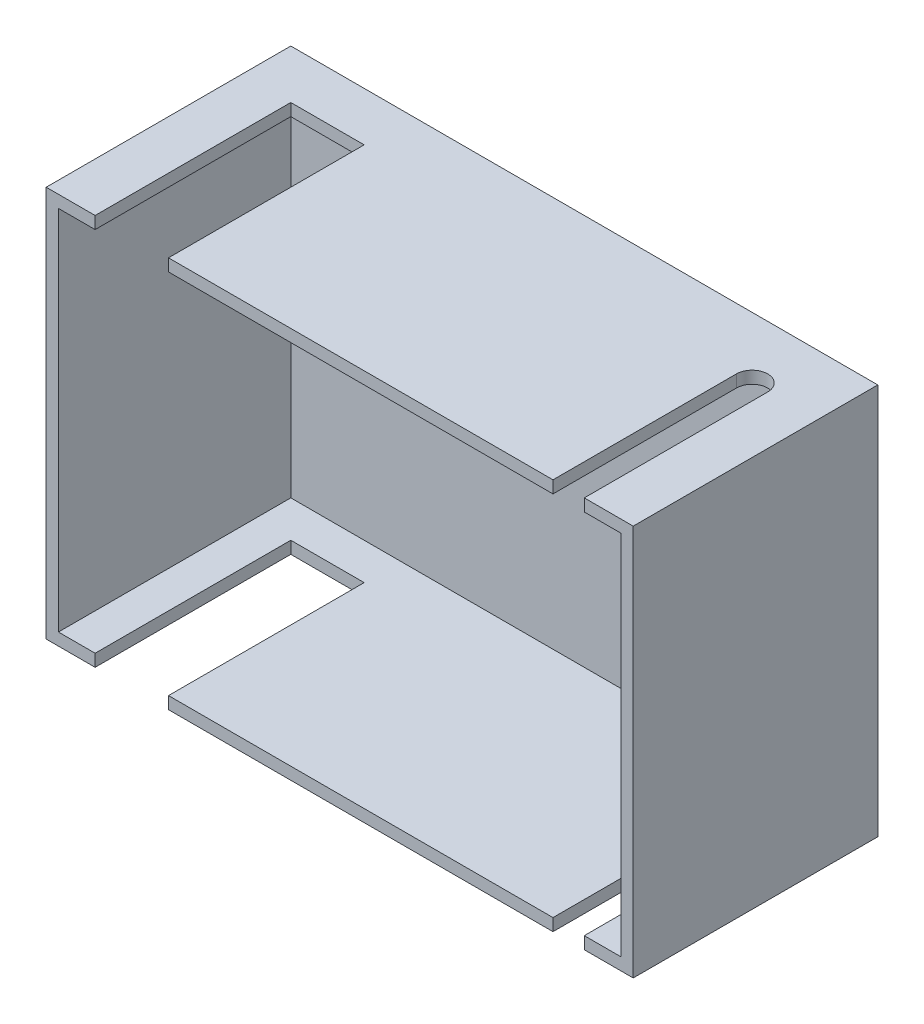
SolidWorks part; units mm, degrees
ref_plane "前基準面" through (0, 0, 0) normal (0, 0, 1) x (1, 0, 0)
ref_plane "上基準面" through (0, 0, 0) normal (0, 1, 0) x (1, 0, 0)
ref_plane "右基準面" through (0, 0, 0) normal (1, 0, 0) x (0, 0, -1)
sketch "草圖1" plane through (0, 0, 0) normal (0, 0, 1) x (1, 0, 0)
  line L1 (-60, 40) -> (60, 40)
  line L2 (-60, 40) -> (-60, -40)
  line L3 (-60, -40) -> (60, -40)
  line L4 (60, 40) -> (60, -40)
  line L5 (-60, 40) -> (60, -40) construction
  line L6 (-60, -40) -> (60, 40) construction
  point P0 (0, 0)
  dimension "D1" = 120
  dimension "D2" = 80
extrude "填料-伸長1" add sketch "草圖1" along normal blind 50
shell "薄殼1" thickness 2.5
sketch "草圖2" plane through (0, -40, 0) normal (0, -1, 0) x (1, 0, 0)
  line L1 (-50, 50) -> (-35, 50)
  line L2 (-50, 50) -> (-50, 10)
  line L3 (-50, 10) -> (-35, 10)
  line L4 (-35, 50) -> (-35, 10)
  line L5 (-50, 50) -> (-35, 10) construction
  line L6 (-50, 10) -> (-35, 50) construction
  line L7 (-60, 50) -> (60, 50) construction
  line L8 (-60, 50) -> (-60, 0) construction
  point P0 (-42.5, 30)
  dimension "D1" = 15
  dimension "D2" = 40
  dimension "D3" = 0
  dimension "D4" = 10
extrude "除料-伸長1" cut sketch "草圖2" against normal blind 90
sketch "草圖3" plane through (0, -40, 0) normal (0, -1, 0) x (1, 0, 0)
  line L0 (43.6, 12.5) -> (43.6, 50)
  line L2 (-35, 50) -> (60, 50) construction
  line L3 (50, 12.5) -> (50, 50)
  line L4 (60, 50) -> (60, 0) construction
  line L5 (-60, 0) -> (60, 0) construction
  arc A0 (43.6, 12.5) -> (50, 12.5) centre (46.8, 12.5) ccw
  dimension "D2" = 3.2
  dimension "D1" = 10
  dimension "D3" = 12.5
extrude "除料-伸長3" cut sketch "草圖3" against normal through all and the other way through all
